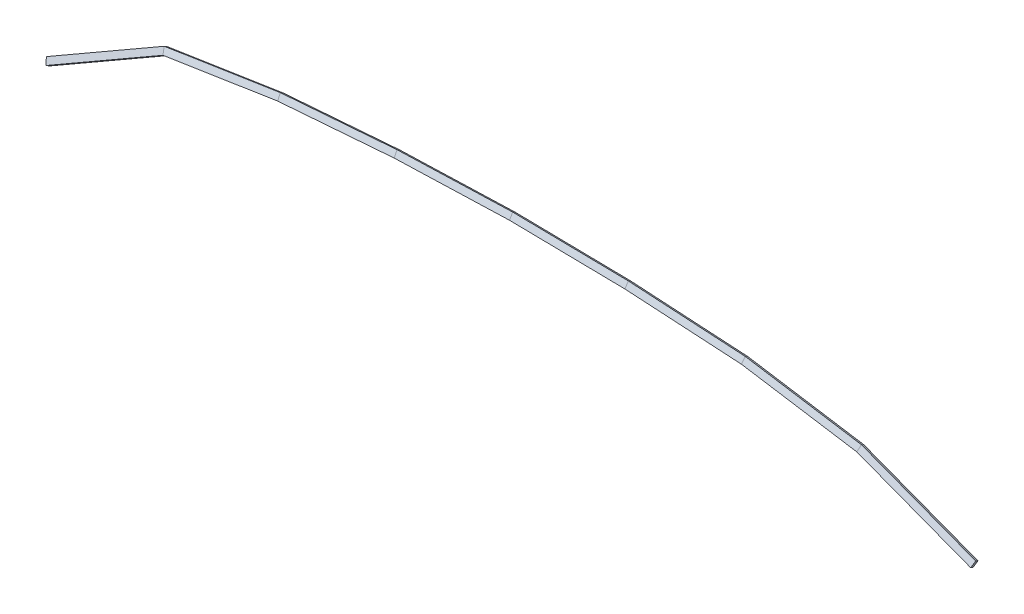
SolidWorks part; units mm, degrees
ref_plane "Front Plane" through (0, 0, 0) normal (0, 0, 1) x (1, 0, 0)
ref_plane "Top Plane" through (0, 0, 0) normal (0, 1, 0) x (1, 0, 0)
ref_plane "Right Plane" through (0, 0, 0) normal (1, 0, 0) x (0, 0, -1)
sketch "Sketch1" plane through (0, 0, 133.35) normal (0, 0, 1) x (1, 0, 0)
  line L0 (-591.5546, -51.2435) -> (-784.0716, -162.1174) construction
  line L1 (-402.166, -22.0956) -> (-591.5546, -51.2435) construction
  line L2 (-211.416, -7.5123) -> (-402.166, -22.0956) construction
  line L3 (-22.6652, -1.2703) -> (-211.416, -7.5123) construction
  line L4 (-22.6652, -1.2703) -> (166.1651, -4.2609) construction
  line L5 (166.1651, -4.2609) -> (357.1251, -15.5363) construction
  line L6 (357.1251, -15.5363) -> (546.7752, -45.5381) construction
  line L7 (546.7752, -45.5381) -> (733.4834, -116.6542) construction
  line L16 (-591.5546, -51.2435) -> (-784.0716, -162.1174)
  line L17 (-402.166, -22.0956) -> (-591.5546, -51.2435)
  line L18 (-211.416, -7.5123) -> (-402.166, -22.0956)
  line L19 (-22.6652, -1.2703) -> (-211.416, -7.5123)
  line L20 (-22.6652, -1.2703) -> (166.1651, -4.2609)
  line L21 (166.1651, -4.2609) -> (357.1251, -15.5363)
  line L22 (357.1251, -15.5363) -> (546.7752, -45.5381)
  line L23 (546.7752, -45.5381) -> (733.4834, -116.6542)
sketch "Sketch2" plane through (0, 0, 0) normal (1, 0, 0) x (0, 0, -1)
  line L0 (-133.35, -1.6389) -> (-128.7526, -4.2932)
  line L1 (-128.7526, -4.2932) -> (-133.9342, -13.268)
  line L2 (-133.9342, -13.268) -> (-138.5316, -10.6137)
  line L3 (-138.5316, -10.6137) -> (-133.35, -1.6389)
  line L4 (-133.35, -1.2703) -> (-133.35, -4.2609) construction
  line L5 (-133.35, -1.6389) -> (-133.35, 7.2562) construction
  dimension "D1" = 5.3086
  dimension "D2" = 10.3632
  dimension "D3" = 30
sweep "Sweep1" add profiles "Sketch2" path "Sketch1"
sketch "Sketch3" plane through (71.8879, 6.0598, 1117.6) normal (0.9999, -0.0158, 0) x (0, 0, -1)
  line L0 (988.0534, -24.0665) -> (1009.9707, -62.0283) construction
  line L1 (1015.8095, -65.2033) -> (1015.47, -65.2033) construction
  line L2 (1015.8095, -59.882) -> (1015.8095, -65.2033) construction
  line L3 (1015.8095, -59.882) -> (1010.7295, -59.882) construction
  line L4 (1010.7295, -54.802) -> (1010.7295, -59.882) construction
  line L5 (1010.7295, -54.802) -> (1015.8095, -54.802) construction
  line L6 (1015.8095, -50.0268) -> (1015.8095, -54.802) construction
  line L7 (1015.8095, -50.0268) -> (1018.3495, -50.0268) construction
  line L8 (978.8082, -17.8795) -> (984.1803, -8.5759) construction
  line L9 (984.1803, -8.5759) -> (989.1076, -11.4203) construction
  line L10 (989.1076, -11.4203) -> (983.7355, -20.724) construction
  line L12 (978.8082, -17.8795) -> (976.4114, -19.2631) construction
  line L13 (966.4634, -10.0965) -> (971.74, -10.0965) construction
  line L14 (971.5434, -7.5565) -> (963.9234, -7.5565) construction
  line L15 (971.5434, -7.5565) -> (990.8488, -7.5565) construction
  line L16 (990.8488, -23.8281) -> (990.8488, -7.5565) construction
  line L23 (1018.3495, -50.2173) -> (1018.3495, -48.7568) construction
  line L24 (1017.0795, -47.4868) -> (1004.5081, -47.4868) construction
  line L25 (1004.5081, -47.4868) -> (990.8488, -23.8281) construction
  line L26 (983.7355, -20.724) -> (983.7354, -23.4918) construction
  line L31 (988.0534, -24.0665) -> (1009.9707, -62.0283)
  line L32 (1015.8095, -65.2033) -> (1015.47, -65.2033)
  line L33 (1015.8095, -59.882) -> (1015.8095, -65.2033)
  line L34 (1015.8095, -59.882) -> (1010.7295, -59.882)
  line L35 (1010.7295, -54.802) -> (1010.7295, -59.882)
  line L36 (1010.7295, -54.802) -> (1015.8095, -54.802)
  line L37 (1015.8095, -50.0268) -> (1015.8095, -54.802)
  line L38 (1015.8095, -50.0268) -> (1018.3495, -50.0268)
  line L39 (978.8082, -17.8795) -> (984.1803, -8.5759)
  line L40 (984.1803, -8.5759) -> (989.1076, -11.4203)
  line L41 (989.1076, -11.4203) -> (983.7355, -20.724)
  line L43 (978.8082, -17.8795) -> (976.4114, -19.2631)
  line L44 (966.4634, -10.0965) -> (971.74, -10.0965)
  line L45 (971.5434, -7.5565) -> (963.9234, -7.5565)
  line L46 (971.5434, -7.5565) -> (990.8488, -7.5565)
  line L47 (990.8488, -23.8281) -> (990.8488, -7.5565)
  line L54 (1018.3495, -50.0268) -> (1018.3495, -48.7568)
  line L55 (1017.0795, -47.4868) -> (1004.5081, -47.4868)
  line L56 (1004.5081, -47.4868) -> (990.8488, -23.8281)
  line L57 (983.7355, -20.724) -> (983.7354, -23.4918)
  arc A0 (1009.9707, -62.0283) -> (1015.47, -65.2033) centre (1015.47, -58.8533) ccw construction
  arc A1 (971.74, -10.0965) -> (976.4114, -19.2631) centre (988.0534, -7.5565) ccw construction
  arc A2 (963.9234, -7.5565) -> (966.4634, -10.0965) centre (966.4634, -7.5565) ccw construction
  arc A3 (1018.3495, -48.7568) -> (1017.0795, -47.4868) centre (1017.0795, -48.7568) ccw construction
  arc A4 (983.7354, -23.4918) -> (990.8488, -23.8281) centre (988.0534, -7.5565) ccw construction
  arc A5 (1009.9707, -62.0283) -> (1015.47, -65.2033) centre (1015.47, -58.8533) ccw
  arc A6 (971.74, -10.0965) -> (976.4114, -19.2631) centre (988.0534, -7.5565) ccw
  arc A7 (963.9234, -7.5565) -> (966.4634, -10.0965) centre (966.4634, -7.5565) ccw
  arc A8 (1018.3495, -48.7568) -> (1017.0795, -47.4868) centre (1017.0795, -48.7568) ccw
  arc A9 (983.7354, -23.4918) -> (988.0534, -24.0665) centre (988.0534, -7.5565) ccw
